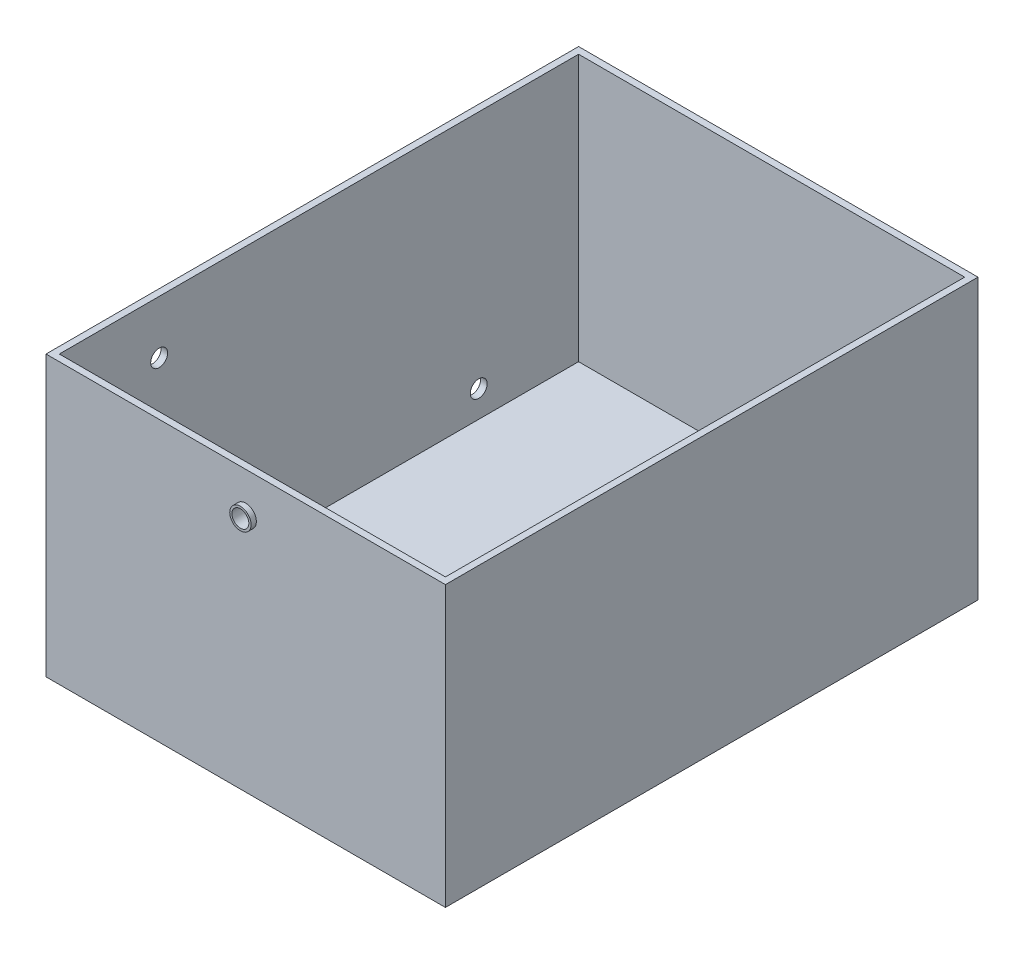
SolidWorks part; units mm, degrees
ref_plane "Front Plane" through (0, 0, 0) normal (0, 0, 1) x (1, 0, 0)
ref_plane "Top Plane" through (0, 0, 0) normal (0, 1, 0) x (1, 0, 0)
ref_plane "Right Plane" through (0, 0, 0) normal (1, 0, 0) x (0, 0, -1)
sketch "Sketch1" plane through (0, 0, 0) normal (0, 1, 0) x (1, 0, 0)
  line L1 (-75, -100) -> (75, -100)
  line L2 (-75, -100) -> (-75, 100)
  line L3 (-75, 100) -> (75, 100)
  line L4 (75, -100) -> (75, 100)
  line L5 (-75, -100) -> (75, 100) construction
  line L6 (-75, 100) -> (75, -100) construction
  point P0 (0, 0)
  dimension "D1" = 200
  dimension "D2" = 150
extrude "Boss-Extrude1" add sketch "Sketch1" along normal blind 5
sketch "Sketch2" plane through (0, 5, 0) normal (0, 1, 0) x (1, 0, 0)
  line L1 (-72.5, -97.5) -> (72.5, -97.5)
  line L2 (-72.5, -97.5) -> (-72.5, 97.5)
  line L3 (-72.5, 97.5) -> (72.5, 97.5)
  line L4 (72.5, -97.5) -> (72.5, 97.5)
  line L5 (-72.5, -97.5) -> (72.5, 97.5) construction
  line L6 (-72.5, 97.5) -> (72.5, -97.5) construction
  line L7 (-75, 100) -> (75, 100)
  line L8 (-75, 100) -> (-75, -100)
  line L9 (-75, -100) -> (75, -100)
  line L10 (75, 100) -> (75, -100)
  line L11 (-75, 100) -> (75, -100) construction
  line L12 (-75, -100) -> (75, 100) construction
  point P0 (0, 0)
  point P6 (0, 0)
  dimension "D1" = 145
  dimension "D2" = 195
extrude "Boss-Extrude2" add sketch "Sketch2" along normal blind 100
sketch "Sketch3" plane through (0, 0, 100) normal (0, 0, 1) x (1, 0, 0)
  line L0 (-75, 105) -> (75, 105) construction
  circle A0 centre (0, 90) radius 3.175
  dimension "D2" = 6.35
  dimension "D1" = 15
extrude "Cut-Extrude1" cut sketch "Sketch3" against normal blind 50
sketch "Sketch4" plane through (0, 0, 100) normal (0, 0, 1) x (1, 0, 0)
  circle A0 centre (0, 90) radius 3.175
  circle A1 centre (0, 90) radius 4
  dimension "D1" = 8
extrude "Boss-Extrude3" add sketch "Sketch4" along normal blind 2
sketch "Sketch5" plane through (0, 0, -100) normal (0, 0, -1) x (-1, 0, 0)
  line L0 (-75, 0) -> (75, 0) construction
  circle A0 centre (0, 10) radius 3.175
  dimension "D2" = 6.35
  dimension "D1" = 10
extrude "Cut-Extrude2" cut sketch "Sketch5" against normal blind 14
sketch "Sketch6" plane through (0, 0, -100) normal (0, 0, -1) x (-1, 0, 0)
  circle A0 centre (0, 10) radius 3.175
  circle A1 centre (0, 10) radius 4
  dimension "D1" = 8
extrude "Boss-Extrude4" add sketch "Sketch6" along normal blind 2
sketch "Sketch7" plane through (-75, 0, 0) normal (-1, 0, 0) x (0, 0, 1)
  circle A0 centre (-60, 15) radius 3.175
  circle A1 centre (60, 85) radius 3.175
extrude "Cut-Extrude3" cut sketch "Sketch7" against normal blind 10
